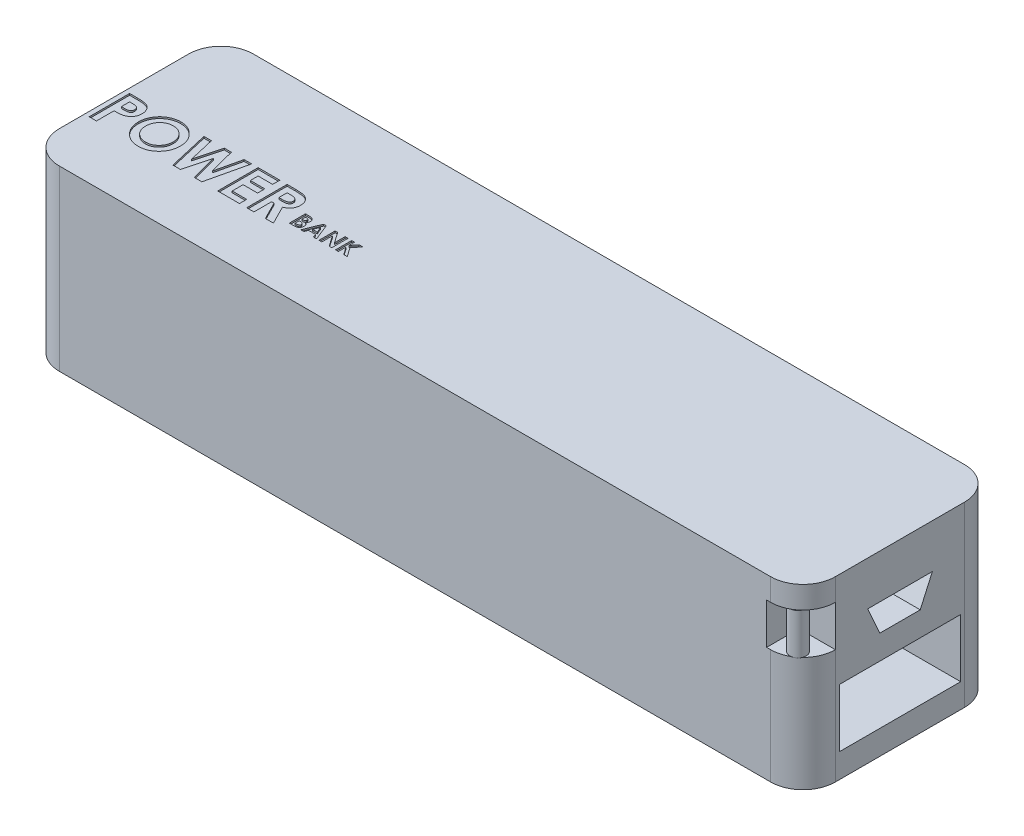
SolidWorks part; units mm, degrees
material "ABS"
ref_plane "Front Plane" through (0, 0, 0) normal (0, 0, 1) x (1, 0, 0)
ref_plane "Top Plane" through (0, 0, 0) normal (0, 1, 0) x (1, 0, 0)
ref_plane "Right Plane" through (0, 0, 0) normal (1, 0, 0) x (0, 0, -1)
sketch "Sketch1" plane through (0, 0, 0) normal (0, 1, 0) x (1, 0, 0)
  line L1 (-44, -12) -> (44, -12)
  line L2 (-48, -8) -> (-48, 8)
  line L3 (-44, 12) -> (44, 12)
  line L4 (48, -8) -> (48, 8)
  line L5 (-48, -12) -> (48, 12) construction
  line L6 (-48, 12) -> (48, -12) construction
  arc A0 (-44, -12) -> (-48, -8) centre (-44, -8) cw
  arc A1 (44, -12) -> (48, -8) centre (44, -8) ccw
  arc A2 (44, 12) -> (48, 8) centre (44, 8) cw
  arc A3 (-48, 8) -> (-44, 12) centre (-44, 8) cw
  point P0 (0, 0)
  dimension "D3" = 4
  dimension "D1" = 24
  dimension "D2" = 96
extrude "Boss-Extrude1" add sketch "Sketch1" along normal blind 22
sketch "Sketch2" plane through (0, 22, 0) normal (0, 1, 0) x (1, 0, 0)
  line L0 (-48, -4.8806) -> (4.5219, -4.8806) construction
  line L1 (-48, 8) -> (-48, -8) construction
  text T0 "<b>POWER</b>" font "Century Gothic" height 5
extrude "Cut-Extrude1" cut sketch "Sketch2" against normal blind 0.2
sketch "Sketch3" plane through (0, 22, 0) normal (0, 1, 0) x (1, 0, 0)
  line L0 (-23.8803, -3.8961) -> (-12.5235, -3.8961) construction
  text T0 "<b>BANK</b>" font "Century Gothic" height 2
extrude "Cut-Extrude2" cut sketch "Sketch3" against normal blind 0.2
sketch "Sketch4" plane through (48, 0, 0) normal (1, 0, 0) x (0, 0, -1)
  line L0 (0, 0) -> (0, 22) construction
  line L1 (-7.5, 10.2) -> (7.5, 10.2)
  line L2 (-7.5, 10.2) -> (-7.5, 3)
  line L3 (-7.5, 3) -> (7.5, 3)
  line L4 (7.5, 10.2) -> (7.5, 3)
  line L5 (-8, 0) -> (8, 0) construction
  line L6 (-8, 22) -> (8, 22) construction
  point P11 (0, 3)
  point P12 (0, 10.2)
  dimension "D1" = 7.2
  dimension "D2" = 7.5
  dimension "D3" = 3
extrude "Cut-Extrude3" cut sketch "Sketch4" against normal blind 10
sketch "Sketch5" plane through (48, 0, 0) normal (1, 0, 0) x (0, 0, -1)
  line L0 (0, 22) -> (0, 0) construction
  line L1 (-8, 22) -> (8, 22) construction
  line L2 (-8, 0) -> (8, 0) construction
  line L3 (-4, 16.55) -> (4, 16.55)
  line L4 (4, 16.55) -> (2.5, 13.2)
  line L5 (2.5, 13.2) -> (-2.5, 13.2)
  line L6 (-2.5, 13.2) -> (-4, 16.55)
  line L7 (7.5, 10.2) -> (-7.5, 10.2) construction
  point P8 (0, 16.55)
  point P11 (0, 13.2)
  dimension "D1" = 8
  dimension "D2" = 5
  dimension "D3" = 3
  dimension "D4" = 3.35
extrude "Cut-Extrude4" cut sketch "Sketch5" against normal blind 10
sketch "Sketch6" plane through (0, 0, 12) normal (0, 0, 1) x (1, 0, 0)
  line L0 (48, 22) -> (48, 0) construction
  line L1 (43.5, 19.249) -> (48, 19.249)
  line L2 (43.5, 19.249) -> (43.5, 14.1783)
  line L3 (43.5, 14.1783) -> (48, 14.1783)
  line L4 (48, 19.249) -> (48, 14.1783)
  dimension "D1" = 4.5
extrude "Cut-Extrude5" cut sketch "Sketch6" against normal up to vertex (4 mm away)
sketch "Sketch7" plane through (0, 14.1783, 0) normal (0, 1, 0) x (1, 0, 0)
  circle A0 centre (45.8692, -10.4866) radius 1
  dimension "D1" = 2
extrude "Boss-Extrude3" add sketch "Sketch7" along normal up to surface (5.0707 mm away) up to face at (44.9571, 19.249, 10.2071)
